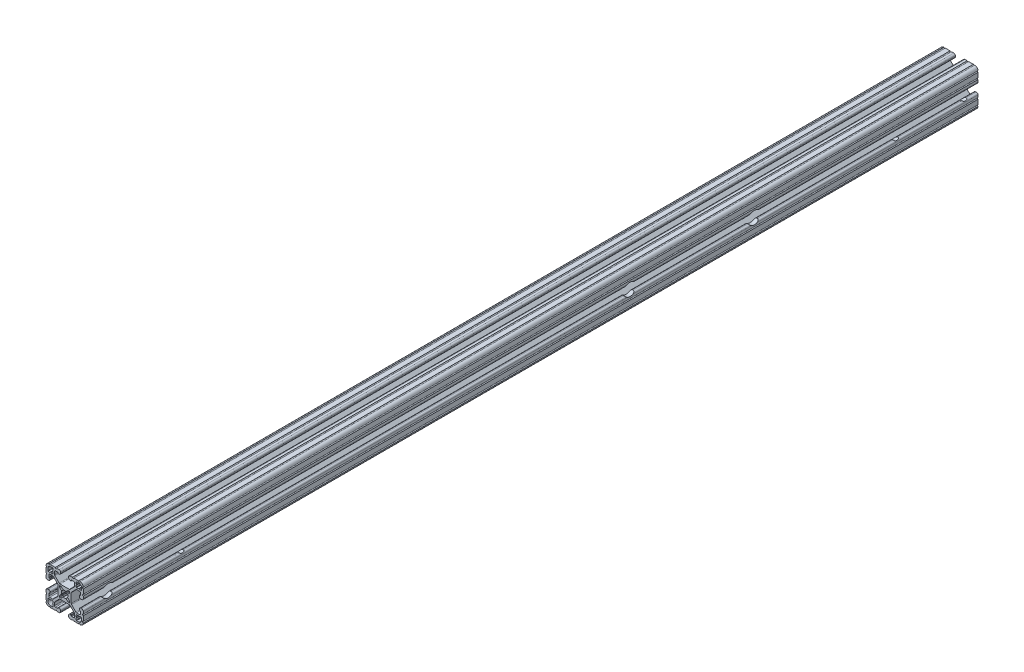
SolidWorks part; units mm, degrees
ref_plane "Front Plane" through (0, 0, 0) normal (0, 0, 1) x (1, 0, 0)
ref_plane "Top Plane" through (0, 0, 0) normal (0, 1, 0) x (1, 0, 0)
ref_plane "Right Plane" through (0, 0, 0) normal (1, 0, 0) x (0, 0, -1)
ref_plane "Plane1" through (0, 0, -2322.576) normal (0, 0, -1) x (-1, 0, 0)
sketch "Sketch1" plane through (0, 0, -2322.576) normal (0, 0, -1) x (-1, 0, 0)
  line L0 (17.2466, 14.4526) -> (17.2466, 12.2428)
  line L1 (16.8656, 11.8618) -> (15.0927, 11.8618)
  line L2 (15.0927, 11.8618) -> (14.5542, 12.4003)
  line L3 (14.5542, 12.4003) -> (14.0157, 11.8618)
  line L4 (14.0157, 11.8618) -> (12.2428, 11.8618)
  line L5 (11.8618, 12.2428) -> (11.8618, 14.0157)
  line L6 (11.8618, 14.0157) -> (12.4003, 14.5542)
  line L7 (12.4003, 14.5542) -> (11.8618, 15.0927)
  line L8 (11.8618, 15.0927) -> (11.8618, 16.8656)
  line L9 (12.2428, 17.2466) -> (14.4526, 17.2466)
  line L10 (17.2466, -12.2428) -> (17.2466, -14.4526)
  line L11 (14.4526, -17.2466) -> (12.2428, -17.2466)
  line L12 (11.8618, -16.8656) -> (11.8618, -15.0927)
  line L13 (11.8618, -15.0927) -> (12.4003, -14.5542)
  line L14 (12.4003, -14.5542) -> (11.8618, -14.0157)
  line L15 (11.8618, -14.0157) -> (11.8618, -12.2428)
  line L16 (12.2428, -11.8618) -> (14.0157, -11.8618)
  line L17 (14.0157, -11.8618) -> (14.5542, -12.4003)
  line L18 (14.5542, -12.4003) -> (15.0927, -11.8618)
  line L19 (15.0927, -11.8618) -> (16.8656, -11.8618)
  line L20 (5.1689, -3.9207) -> (5.1689, -4.9149)
  line L21 (4.9149, -5.1689) -> (3.9207, -5.1689)
  line L22 (3.2921, -4.9085) -> (1.5823, -3.1988)
  line L23 (-1.5823, -3.1988) -> (-3.2921, -4.9085)
  line L24 (-3.9207, -5.1689) -> (-4.9149, -5.1689)
  line L25 (-5.1689, -4.9149) -> (-5.1689, -3.9207)
  line L26 (-4.9085, -3.2921) -> (-3.1988, -1.5823)
  line L27 (-3.1988, 1.5823) -> (-4.9085, 3.2921)
  line L28 (-5.1689, 3.9207) -> (-5.1689, 4.9149)
  line L29 (-4.9149, 5.1689) -> (-3.9207, 5.1689)
  line L30 (-3.2921, 4.9085) -> (-1.5823, 3.1988)
  line L31 (1.5823, 3.1988) -> (3.2921, 4.9085)
  line L32 (3.9207, 5.1689) -> (4.9149, 5.1689)
  line L33 (5.1689, 4.9149) -> (5.1689, 3.9207)
  line L34 (4.9085, 3.2921) -> (3.1988, 1.5823)
  line L35 (3.1988, -1.5823) -> (4.9085, -3.2921)
  line L36 (-11.8618, -12.2428) -> (-11.8618, -14.0157)
  line L37 (-11.8618, -14.0157) -> (-12.4003, -14.5542)
  line L38 (-12.4003, -14.5542) -> (-11.8618, -15.0927)
  line L39 (-11.8618, -15.0927) -> (-11.8618, -16.8656)
  line L40 (-12.2428, -17.2466) -> (-14.4526, -17.2466)
  line L41 (-17.2466, -14.4526) -> (-17.2466, -12.2428)
  line L42 (-16.8656, -11.8618) -> (-15.0927, -11.8618)
  line L43 (-15.0927, -11.8618) -> (-14.5542, -12.4003)
  line L44 (-14.5542, -12.4003) -> (-14.0157, -11.8618)
  line L45 (-14.0157, -11.8618) -> (-12.2428, -11.8618)
  line L46 (-11.8618, 16.8656) -> (-11.8618, 15.0927)
  line L47 (-11.8618, 15.0927) -> (-12.4003, 14.5542)
  line L48 (-12.4003, 14.5542) -> (-11.8618, 14.0157)
  line L49 (-11.8618, 14.0157) -> (-11.8618, 12.2428)
  line L50 (-12.2428, 11.8618) -> (-14.0157, 11.8618)
  line L51 (-14.0157, 11.8618) -> (-14.5542, 12.4003)
  line L52 (-14.5542, 12.4003) -> (-15.0927, 11.8618)
  line L53 (-15.0927, 11.8618) -> (-16.8656, 11.8618)
  line L54 (-17.2466, 12.2428) -> (-17.2466, 14.4526)
  line L55 (-14.4526, 17.2466) -> (-12.2428, 17.2466)
  line L56 (19.05, -14.3256) -> (19.05, -9.4996)
  line L57 (19.05, -7.9756) -> (19.05, -5.6388)
  line L58 (17.4752, -4.064) -> (16.5608, -4.064)
  line L59 (14.986, -5.6388) -> (14.986, -6.35)
  line L60 (15.367, -6.731) -> (15.6972, -6.731)
  line L61 (16.0782, -7.112) -> (16.0782, -9.398)
  line L62 (15.1892, -10.287) -> (12.3756, -10.287)
  line L63 (11.4776, -9.915) -> (7.1157, -5.5531)
  line L64 (6.7437, -4.6551) -> (6.7437, 4.6551)
  line L65 (7.1157, 5.5531) -> (11.4776, 9.915)
  line L66 (12.3756, 10.287) -> (15.1892, 10.287)
  line L67 (16.0782, 9.398) -> (16.0782, 7.112)
  line L68 (15.6972, 6.731) -> (15.367, 6.731)
  line L69 (14.986, 6.35) -> (14.986, 5.6388)
  line L70 (16.5608, 4.064) -> (17.4752, 4.064)
  line L71 (19.05, 5.6388) -> (19.05, 7.9756)
  line L72 (19.05, 9.4996) -> (19.05, 14.3256)
  line L73 (14.3256, 19.05) -> (9.4996, 19.05)
  line L74 (7.9756, 19.05) -> (5.6388, 19.05)
  line L75 (4.064, 17.4752) -> (4.064, 16.5608)
  line L76 (5.6388, 14.986) -> (6.35, 14.986)
  line L77 (6.731, 15.367) -> (6.731, 15.6972)
  line L78 (7.112, 16.0782) -> (9.398, 16.0782)
  line L79 (10.287, 15.1892) -> (10.287, 12.3756)
  line L80 (9.915, 11.4776) -> (5.5531, 7.1157)
  line L81 (4.6551, 6.7437) -> (-4.6551, 6.7437)
  line L82 (-5.5531, 7.1157) -> (-9.915, 11.4776)
  line L83 (-10.287, 12.3756) -> (-10.287, 15.1892)
  line L84 (-9.398, 16.0782) -> (-7.112, 16.0782)
  line L85 (-6.731, 15.6972) -> (-6.731, 15.367)
  line L86 (-6.35, 14.986) -> (-5.6388, 14.986)
  line L87 (-4.064, 16.5608) -> (-4.064, 17.4752)
  line L88 (-5.6388, 19.05) -> (-7.9756, 19.05)
  line L89 (-9.4996, 19.05) -> (-14.3256, 19.05)
  line L90 (-19.05, 14.3256) -> (-19.05, 9.4996)
  line L91 (-19.05, 7.9756) -> (-19.05, 5.6388)
  line L92 (-17.4752, 4.064) -> (-16.5608, 4.064)
  line L93 (-14.986, 5.6388) -> (-14.986, 6.35)
  line L94 (-15.367, 6.731) -> (-15.6972, 6.731)
  line L95 (-16.0782, 7.112) -> (-16.0782, 9.398)
  line L96 (-15.1892, 10.287) -> (-12.3756, 10.287)
  line L97 (-11.4776, 9.915) -> (-7.1157, 5.5531)
  line L98 (-6.7437, 4.6551) -> (-6.7437, -4.6551)
  line L99 (-7.1157, -5.5531) -> (-11.4776, -9.915)
  line L100 (-12.3756, -10.287) -> (-15.1892, -10.287)
  line L101 (-16.0782, -9.398) -> (-16.0782, -7.112)
  line L102 (-15.6972, -6.731) -> (-15.367, -6.731)
  line L103 (-14.986, -6.35) -> (-14.986, -5.6388)
  line L104 (-16.5608, -4.064) -> (-17.4752, -4.064)
  line L105 (-19.05, -5.6388) -> (-19.05, -7.9756)
  line L106 (-19.05, -9.4996) -> (-19.05, -14.3256)
  line L107 (-14.3256, -19.05) -> (-9.4996, -19.05)
  line L108 (-7.9756, -19.05) -> (-5.6388, -19.05)
  line L109 (-4.064, -17.4752) -> (-4.064, -16.5608)
  line L110 (-5.6388, -14.986) -> (-6.35, -14.986)
  line L111 (-6.731, -15.367) -> (-6.731, -15.6972)
  line L112 (-7.112, -16.0782) -> (-9.398, -16.0782)
  line L113 (-10.287, -15.1892) -> (-10.287, -12.3756)
  line L114 (-9.915, -11.4776) -> (-5.5531, -7.1157)
  line L115 (-4.6551, -6.7437) -> (4.6551, -6.7437)
  line L116 (5.5531, -7.1157) -> (9.915, -11.4776)
  line L117 (10.287, -12.3756) -> (10.287, -15.1892)
  line L118 (9.398, -16.0782) -> (7.112, -16.0782)
  line L119 (6.731, -15.6972) -> (6.731, -15.367)
  line L120 (6.35, -14.986) -> (5.6388, -14.986)
  line L121 (4.064, -16.5608) -> (4.064, -17.4752)
  line L122 (5.6388, -19.05) -> (7.9756, -19.05)
  line L123 (9.4996, -19.05) -> (14.3256, -19.05)
  arc A0 (17.2466, 12.2428) -> (16.8656, 11.8618) centre (16.8656, 12.2428) cw
  arc A1 (12.2428, 11.8618) -> (11.8618, 12.2428) centre (12.2428, 12.2428) cw
  arc A2 (11.8618, 16.8656) -> (12.2428, 17.2466) centre (12.2428, 16.8656) cw
  arc A3 (14.4526, 17.2466) -> (17.2466, 14.4526) centre (14.4526, 14.4526) cw
  arc A4 (17.2466, -14.4526) -> (14.4526, -17.2466) centre (14.4526, -14.4526) cw
  arc A5 (12.2428, -17.2466) -> (11.8618, -16.8656) centre (12.2428, -16.8656) cw
  arc A6 (11.8618, -12.2428) -> (12.2428, -11.8618) centre (12.2428, -12.2428) cw
  arc A7 (16.8656, -11.8618) -> (17.2466, -12.2428) centre (16.8656, -12.2428) cw
  arc A8 (5.1689, -4.9149) -> (4.9149, -5.1689) centre (4.9149, -4.9149) cw
  arc A9 (3.9207, -5.1689) -> (3.2921, -4.9085) centre (3.9207, -4.2799) cw
  arc A10 (1.5823, -3.1988) -> (1.178, -3.1119) centre (1.3129, -3.4682) ccw
  arc A11 (1.178, -3.1119) -> (-1.178, -3.1119) centre (0, 0) cw
  arc A12 (-1.178, -3.1119) -> (-1.5823, -3.1988) centre (-1.3129, -3.4682) ccw
  arc A13 (-3.2921, -4.9085) -> (-3.9207, -5.1689) centre (-3.9207, -4.2799) cw
  arc A14 (-4.9149, -5.1689) -> (-5.1689, -4.9149) centre (-4.9149, -4.9149) cw
  arc A15 (-5.1689, -3.9207) -> (-4.9085, -3.2921) centre (-4.2799, -3.9207) cw
  arc A16 (-3.1988, -1.5823) -> (-3.1119, -1.178) centre (-3.4682, -1.3129) ccw
  arc A17 (-3.1119, -1.178) -> (-3.1119, 1.178) centre (0, 0) cw
  arc A18 (-3.1119, 1.178) -> (-3.1988, 1.5823) centre (-3.4682, 1.3129) ccw
  arc A19 (-4.9085, 3.2921) -> (-5.1689, 3.9207) centre (-4.2799, 3.9207) cw
  arc A20 (-5.1689, 4.9149) -> (-4.9149, 5.1689) centre (-4.9149, 4.9149) cw
  arc A21 (-3.9207, 5.1689) -> (-3.2921, 4.9085) centre (-3.9207, 4.2799) cw
  arc A22 (-1.5823, 3.1988) -> (-1.178, 3.1119) centre (-1.3129, 3.4682) ccw
  arc A23 (-1.178, 3.1119) -> (1.178, 3.1119) centre (0, 0) cw
  arc A24 (1.178, 3.1119) -> (1.5823, 3.1988) centre (1.3129, 3.4682) ccw
  arc A25 (3.2921, 4.9085) -> (3.9207, 5.1689) centre (3.9207, 4.2799) cw
  arc A26 (4.9149, 5.1689) -> (5.1689, 4.9149) centre (4.9149, 4.9149) cw
  arc A27 (5.1689, 3.9207) -> (4.9085, 3.2921) centre (4.2799, 3.9207) cw
  arc A28 (3.1988, 1.5823) -> (3.1119, 1.178) centre (3.4682, 1.3129) ccw
  arc A29 (3.1119, 1.178) -> (3.1119, -1.178) centre (0, 0) cw
  arc A30 (3.1119, -1.178) -> (3.1988, -1.5823) centre (3.4682, -1.3129) ccw
  arc A31 (4.9085, -3.2921) -> (5.1689, -3.9207) centre (4.2799, -3.9207) cw
  arc A32 (-11.8618, -16.8656) -> (-12.2428, -17.2466) centre (-12.2428, -16.8656) cw
  arc A33 (-14.4526, -17.2466) -> (-17.2466, -14.4526) centre (-14.4526, -14.4526) cw
  arc A34 (-17.2466, -12.2428) -> (-16.8656, -11.8618) centre (-16.8656, -12.2428) cw
  arc A35 (-12.2428, -11.8618) -> (-11.8618, -12.2428) centre (-12.2428, -12.2428) cw
  arc A36 (-12.2428, 17.2466) -> (-11.8618, 16.8656) centre (-12.2428, 16.8656) cw
  arc A37 (-11.8618, 12.2428) -> (-12.2428, 11.8618) centre (-12.2428, 12.2428) cw
  arc A38 (-16.8656, 11.8618) -> (-17.2466, 12.2428) centre (-16.8656, 12.2428) cw
  arc A39 (-17.2466, 14.4526) -> (-14.4526, 17.2466) centre (-14.4526, 14.4526) cw
  arc A40 (19.05, -9.4996) -> (19.05, -7.9756) centre (19.05, -8.7376) cw
  arc A41 (19.05, -5.6388) -> (17.4752, -4.064) centre (17.4752, -5.6388) ccw
  arc A42 (16.5608, -4.064) -> (14.986, -5.6388) centre (16.5608, -5.6388) ccw
  arc A43 (14.986, -6.35) -> (15.367, -6.731) centre (15.367, -6.35) ccw
  arc A44 (15.6972, -6.731) -> (16.0782, -7.112) centre (15.6972, -7.112) cw
  arc A45 (16.0782, -9.398) -> (15.1892, -10.287) centre (15.1892, -9.398) cw
  arc A46 (12.3756, -10.287) -> (11.4776, -9.915) centre (12.3756, -9.017) cw
  arc A47 (7.1157, -5.5531) -> (6.7437, -4.6551) centre (8.0137, -4.6551) cw
  arc A48 (6.7437, 4.6551) -> (7.1157, 5.5531) centre (8.0137, 4.6551) cw
  arc A49 (11.4776, 9.915) -> (12.3756, 10.287) centre (12.3756, 9.017) cw
  arc A50 (15.1892, 10.287) -> (16.0782, 9.398) centre (15.1892, 9.398) cw
  arc A51 (16.0782, 7.112) -> (15.6972, 6.731) centre (15.6972, 7.112) cw
  arc A52 (15.367, 6.731) -> (14.986, 6.35) centre (15.367, 6.35) ccw
  arc A53 (14.986, 5.6388) -> (16.5608, 4.064) centre (16.5608, 5.6388) ccw
  arc A54 (17.4752, 4.064) -> (19.05, 5.6388) centre (17.4752, 5.6388) ccw
  arc A55 (19.05, 7.9756) -> (19.05, 9.4996) centre (19.05, 8.7376) cw
  arc A56 (19.05, 14.3256) -> (19.0499, 15.8496) centre (19.05, 15.0876) cw
  arc A57 (19.0499, 15.8496) -> (15.8496, 19.0499) centre (15.875, 15.875) ccw
  arc A58 (15.8496, 19.0499) -> (14.3256, 19.05) centre (15.0876, 19.05) cw
  arc A59 (9.4996, 19.05) -> (7.9756, 19.05) centre (8.7376, 19.05) cw
  arc A60 (5.6388, 19.05) -> (4.064, 17.4752) centre (5.6388, 17.4752) ccw
  arc A61 (4.064, 16.5608) -> (5.6388, 14.986) centre (5.6388, 16.5608) ccw
  arc A62 (6.35, 14.986) -> (6.731, 15.367) centre (6.35, 15.367) ccw
  arc A63 (6.731, 15.6972) -> (7.112, 16.0782) centre (7.112, 15.6972) cw
  arc A64 (9.398, 16.0782) -> (10.287, 15.1892) centre (9.398, 15.1892) cw
  arc A65 (10.287, 12.3756) -> (9.915, 11.4776) centre (9.017, 12.3756) cw
  arc A66 (5.5531, 7.1157) -> (4.6551, 6.7437) centre (4.6551, 8.0137) cw
  arc A67 (-4.6551, 6.7437) -> (-5.5531, 7.1157) centre (-4.6551, 8.0137) cw
  arc A68 (-9.915, 11.4776) -> (-10.287, 12.3756) centre (-9.017, 12.3756) cw
  arc A69 (-10.287, 15.1892) -> (-9.398, 16.0782) centre (-9.398, 15.1892) cw
  arc A70 (-7.112, 16.0782) -> (-6.731, 15.6972) centre (-7.112, 15.6972) cw
  arc A71 (-6.731, 15.367) -> (-6.35, 14.986) centre (-6.35, 15.367) ccw
  arc A72 (-5.6388, 14.986) -> (-4.064, 16.5608) centre (-5.6388, 16.5608) ccw
  arc A73 (-4.064, 17.4752) -> (-5.6388, 19.05) centre (-5.6388, 17.4752) ccw
  arc A74 (-7.9756, 19.05) -> (-9.4996, 19.05) centre (-8.7376, 19.05) cw
  arc A75 (-14.3256, 19.05) -> (-15.8496, 19.0499) centre (-15.0876, 19.05) cw
  arc A76 (-15.8496, 19.0499) -> (-19.0499, 15.8496) centre (-15.875, 15.875) ccw
  arc A77 (-19.0499, 15.8496) -> (-19.05, 14.3256) centre (-19.05, 15.0876) cw
  arc A78 (-19.05, 9.4996) -> (-19.05, 7.9756) centre (-19.05, 8.7376) cw
  arc A79 (-19.05, 5.6388) -> (-17.4752, 4.064) centre (-17.4752, 5.6388) ccw
  arc A80 (-16.5608, 4.064) -> (-14.986, 5.6388) centre (-16.5608, 5.6388) ccw
  arc A81 (-14.986, 6.35) -> (-15.367, 6.731) centre (-15.367, 6.35) ccw
  arc A82 (-15.6972, 6.731) -> (-16.0782, 7.112) centre (-15.6972, 7.112) cw
  arc A83 (-16.0782, 9.398) -> (-15.1892, 10.287) centre (-15.1892, 9.398) cw
  arc A84 (-12.3756, 10.287) -> (-11.4776, 9.915) centre (-12.3756, 9.017) cw
  arc A85 (-7.1157, 5.5531) -> (-6.7437, 4.6551) centre (-8.0137, 4.6551) cw
  arc A86 (-6.7437, -4.6551) -> (-7.1157, -5.5531) centre (-8.0137, -4.6551) cw
  arc A87 (-11.4776, -9.915) -> (-12.3756, -10.287) centre (-12.3756, -9.017) cw
  arc A88 (-15.1892, -10.287) -> (-16.0782, -9.398) centre (-15.1892, -9.398) cw
  arc A89 (-16.0782, -7.112) -> (-15.6972, -6.731) centre (-15.6972, -7.112) cw
  arc A90 (-15.367, -6.731) -> (-14.986, -6.35) centre (-15.367, -6.35) ccw
  arc A91 (-14.986, -5.6388) -> (-16.5608, -4.064) centre (-16.5608, -5.6388) ccw
  arc A92 (-17.4752, -4.064) -> (-19.05, -5.6388) centre (-17.4752, -5.6388) ccw
  arc A93 (-19.05, -7.9756) -> (-19.05, -9.4996) centre (-19.05, -8.7376) cw
  arc A94 (-19.05, -14.3256) -> (-19.0499, -15.8496) centre (-19.05, -15.0876) cw
  arc A95 (-19.0499, -15.8496) -> (-15.8496, -19.0499) centre (-15.875, -15.875) ccw
  arc A96 (-15.8496, -19.0499) -> (-14.3256, -19.05) centre (-15.0876, -19.05) cw
  arc A97 (-9.4996, -19.05) -> (-7.9756, -19.05) centre (-8.7376, -19.05) cw
  arc A98 (-5.6388, -19.05) -> (-4.064, -17.4752) centre (-5.6388, -17.4752) ccw
  arc A99 (-4.064, -16.5608) -> (-5.6388, -14.986) centre (-5.6388, -16.5608) ccw
  arc A100 (-6.35, -14.986) -> (-6.731, -15.367) centre (-6.35, -15.367) ccw
  arc A101 (-6.731, -15.6972) -> (-7.112, -16.0782) centre (-7.112, -15.6972) cw
  arc A102 (-9.398, -16.0782) -> (-10.287, -15.1892) centre (-9.398, -15.1892) cw
  arc A103 (-10.287, -12.3756) -> (-9.915, -11.4776) centre (-9.017, -12.3756) cw
  arc A104 (-5.5531, -7.1157) -> (-4.6551, -6.7437) centre (-4.6551, -8.0137) cw
  arc A105 (4.6551, -6.7437) -> (5.5531, -7.1157) centre (4.6551, -8.0137) cw
  arc A106 (9.915, -11.4776) -> (10.287, -12.3756) centre (9.017, -12.3756) cw
  arc A107 (10.287, -15.1892) -> (9.398, -16.0782) centre (9.398, -15.1892) cw
  arc A108 (7.112, -16.0782) -> (6.731, -15.6972) centre (7.112, -15.6972) cw
  arc A109 (6.731, -15.367) -> (6.35, -14.986) centre (6.35, -15.367) ccw
  arc A110 (5.6388, -14.986) -> (4.064, -16.5608) centre (5.6388, -16.5608) ccw
  arc A111 (4.064, -17.4752) -> (5.6388, -19.05) centre (5.6388, -17.4752) ccw
  arc A112 (7.9756, -19.05) -> (9.4996, -19.05) centre (8.7376, -19.05) cw
  arc A113 (14.3256, -19.05) -> (15.8496, -19.0499) centre (15.0876, -19.05) cw
  arc A114 (15.8496, -19.0499) -> (19.0499, -15.8496) centre (15.875, -15.875) ccw
  arc A115 (19.0499, -15.8496) -> (19.05, -14.3256) centre (19.05, -15.0876) cw
extrude "Boss-Extrude1" add sketch "Sketch1" against normal blind 914.4
sketch "Sketch3" plane through (19.05, 0, 0) normal (1, 0, 0) x (0, 0, -1)
  line L0 (2322.576, 4.6551) -> (2322.576, -4.6551) construction
  line L2 (1408.176, 4.6551) -> (1408.176, -4.6551) construction
  circle A0 centre (2309.876, 0) radius 4.7625
  circle A1 centre (2240.026, 0) radius 4.7625
  circle A2 centre (2093.976, 0) radius 6.35
  circle A4 centre (1966.976, 0) radius 6.35
  circle A5 centre (1433.576, 0) radius 6.35
  circle A6 centre (1509.776, 0) radius 4.7625
  point P4 (2322.576, 0)
  dimension "D1" = 12.7
  dimension "D2" = 69.85
  dimension "D3" = 228.6
  dimension "D4" = 355.6
  dimension "D5" = 25.4
  dimension "D6" = 101.6
extrude "Cut-Extrude1" cut sketch "Sketch3" against normal through all
